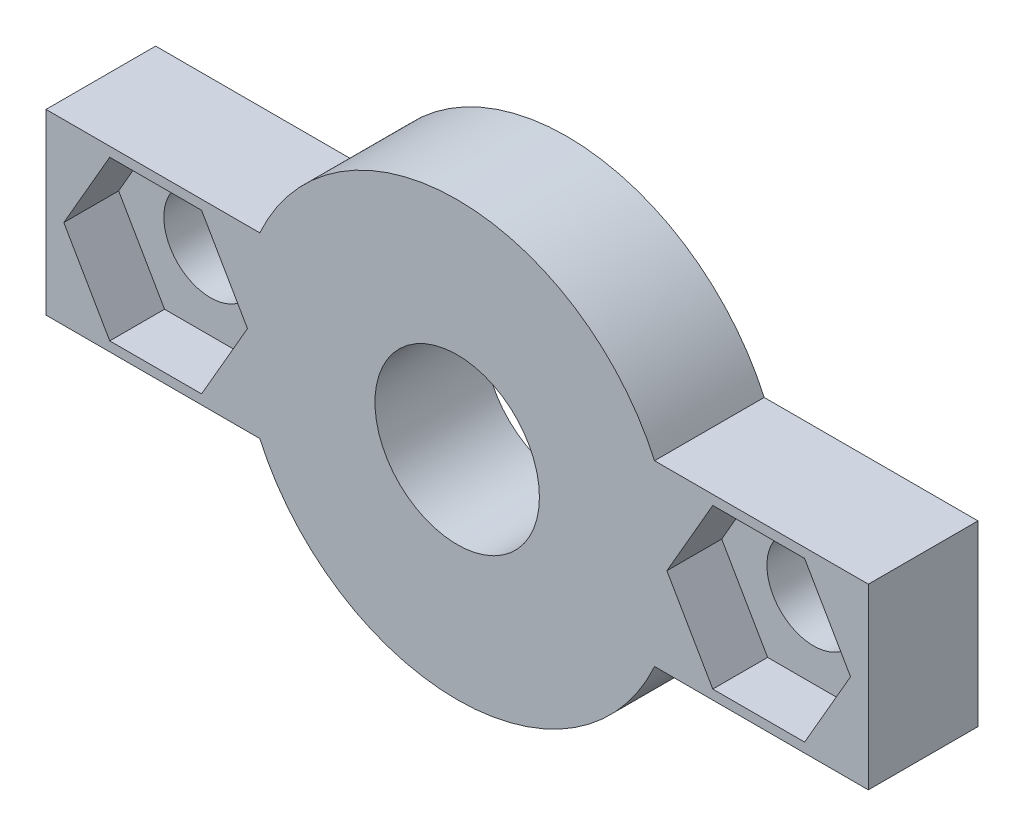
SolidWorks part; units mm, degrees
ref_plane "Alzado" through (0, 0, 0) normal (0, 0, 1) x (1, 0, 0)
ref_plane "Planta" through (0, 0, 0) normal (0, 1, 0) x (1, 0, 0)
ref_plane "Vista lateral" through (0, 0, 0) normal (1, 0, 0) x (0, 0, -1)
sketch "Croquis1" plane through (0, 0, 0) normal (0, 0, 1) x (1, 0, 0)
  line L0 (-7.2005, 3.25) -> (-15, 3.25)
  line L1 (15, -3.25) -> (7.2005, -3.25)
  line L2 (15, -3.25) -> (15, 3.25)
  line L3 (15, 3.25) -> (7.2005, 3.25)
  line L4 (-15, -3.25) -> (-15, 3.25)
  line L5 (15, -3.25) -> (-15, 3.25) construction
  line L6 (15, 3.25) -> (-15, -3.25) construction
  line L9 (-7.2005, -3.25) -> (-15, -3.25)
  arc A0 (-7.2005, -3.25) -> (7.2005, -3.25) centre (0, 0) ccw
  circle A1 centre (0, 0) radius 3
  arc A2 (7.2005, 3.25) -> (-7.2005, 3.25) centre (0, 0) ccw
  dimension "D3" = 6
  dimension "D4" = 7.9
  dimension "D1" = 30
  dimension "D2" = 6.5
extrude "Saliente-Extruir1" add sketch "Croquis1" along normal blind 4
sketch "Croquis2" plane through (0, 0, 4) normal (0, 0, 1) x (1, 0, 0)
  line L0 (-11, 0) -> (11, 0) construction
  line L1 (-15, -3.25) -> (-7.2005, -3.25) construction
  line L2 (-14.35, 0) -> (-12.675, -2.9012)
  line L3 (-12.675, -2.9012) -> (-9.325, -2.9012)
  line L4 (-9.325, -2.9012) -> (-7.65, 0)
  line L5 (-7.65, 0) -> (-9.325, 2.9012)
  line L6 (-9.325, 2.9012) -> (-12.675, 2.9012)
  line L7 (-12.675, 2.9012) -> (-14.35, 0)
  line L8 (14.35, 0) -> (12.675, 2.9012)
  line L9 (12.675, 2.9012) -> (9.325, 2.9012)
  line L10 (9.325, 2.9012) -> (7.65, 0)
  line L11 (7.65, 0) -> (9.325, -2.9012)
  line L12 (9.325, -2.9012) -> (12.675, -2.9012)
  line L13 (12.675, -2.9012) -> (14.35, 0)
  circle A2 centre (-11, 0) radius 3.35 construction
  circle A3 centre (11, 0) radius 3.35 construction
  point P2 (0, 0)
  dimension "D1" = 6.7
  dimension "D2" = 22
extrude "Cortar-Extruir1" cut sketch "Croquis2" against normal blind 2
sketch "Croquis3" plane through (0, 0, 4) normal (0, 0, 1) x (1, 0, 0)
  line L1 (-11, 0) -> (11, 0) construction
  circle A0 centre (-11, 0) radius 1.7
  circle A1 centre (11, 0) radius 1.7
  point P2 (0, 0)
  point P5 (0, 0)
  point P6 (11.0925, 1.04)
  point P9 (0, 0)
  dimension "D1" = 3.4
  dimension "D2" = 22
extrude "Cortar-Extruir2" cut sketch "Croquis3" against normal blind 10
